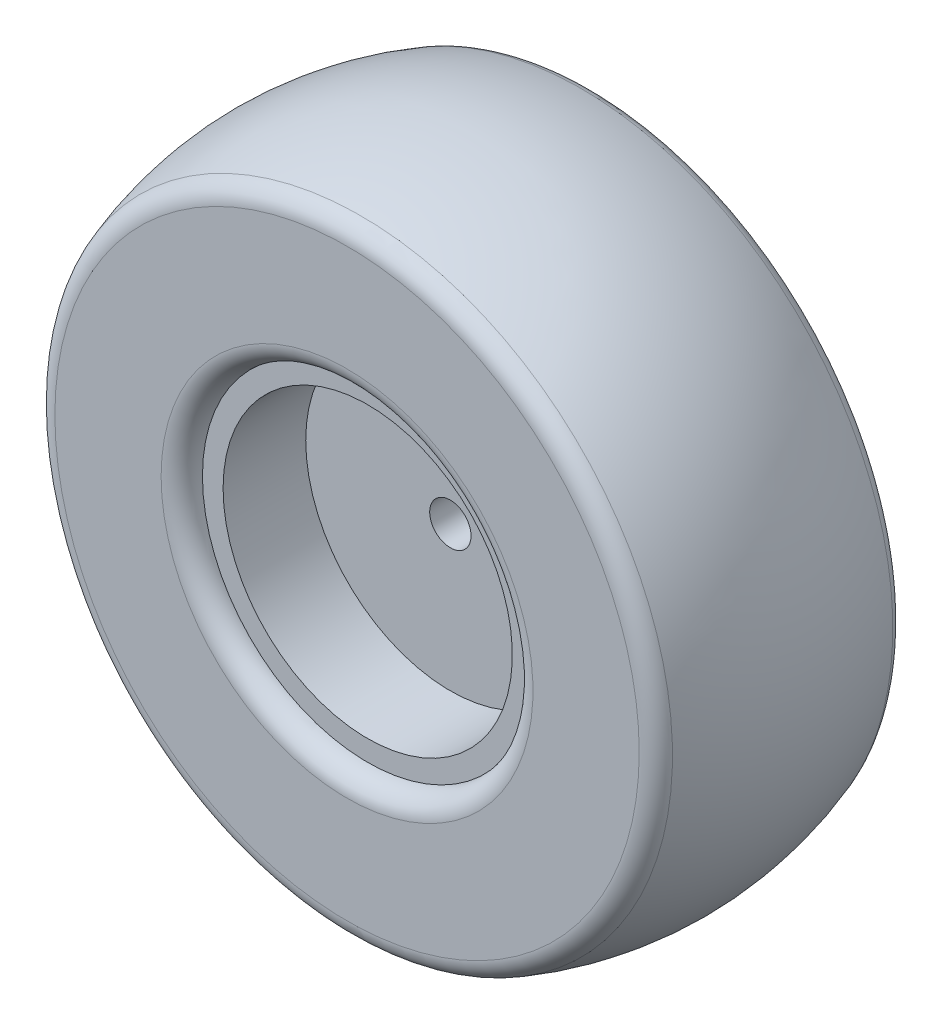
SolidWorks part; units mm, degrees
material "Rubber"
ref_plane "Front Plane" through (0, 0, 0) normal (0, 0, 1) x (1, 0, 0)
ref_plane "Top Plane" through (0, 0, 0) normal (0, 1, 0) x (1, 0, 0)
ref_plane "Right Plane" through (0, 0, 0) normal (1, 0, 0) x (0, 0, -1)
sketch "Sketch1" plane through (0, 0, 0) normal (0, 1, 0) x (1, 0, 0)
  line L0 (0, 0) -> (0, -38.1) construction
  line L1 (0, 0) -> (-101.6, 0) construction
  line L2 (-89.8026, -38.1) -> (-57.15, -38.1)
  line L5 (-101.6, 0) -> (-50.8, 0) construction
  line L6 (-50.8, 31.75) -> (-50.8, -31.75)
  line L7 (-89.8026, 38.1) -> (-57.15, 38.1)
  arc A0 (-95.7894, 33.8667) -> (-95.7894, -33.8667) centre (0, 0) ccw
  arc A1 (-89.8026, -38.1) -> (-95.7894, -33.8667) centre (-89.8026, -31.75) cw
  arc A2 (-57.15, -38.1) -> (-50.8, -31.75) centre (-57.15, -31.75) ccw
  arc A3 (-57.15, 38.1) -> (-50.8, 31.75) centre (-57.15, 31.75) cw
  arc A4 (-89.8026, 38.1) -> (-95.7894, 33.8667) centre (-89.8026, 31.75) ccw
  dimension "D1" = 76.2
  dimension "D4" = 6.35
  dimension "D5" = 6.35
  dimension "D3" = 50.8
revolve "Revolve1" add sketch "Sketch1" angle 360 about L0
sketch "Sketch2" plane through (0, 0, 0) normal (0, 1, 0) x (1, 0, 0)
  line L0 (-50.8, 31.75) -> (-44.45, 31.75)
  line L1 (-50.8, 31.75) -> (50.8, 31.75) construction
  line L2 (-44.45, 31.75) -> (-44.45, 6.35)
  line L3 (-57.15, 38.1) -> (-89.8026, 38.1)
  line L4 (-50.8, -31.75) -> (-50.8, 31.75)
  line L5 (-89.8026, -38.1) -> (-57.15, -38.1)
  line L6 (-57.15, 38.1) -> (-89.8026, 38.1)
  line L7 (-50.8, -31.75) -> (-50.8, 31.75)
  line L8 (-89.8026, -38.1) -> (-57.15, -38.1)
  line L9 (-44.45, 6.35) -> (0, 6.35)
  line L10 (0, 6.35) -> (0, -6.35)
  line L12 (-44.45, -6.35) -> (0, -6.35)
  line L13 (-44.45, -31.75) -> (-44.45, -6.35)
  line L15 (-50.8, -31.75) -> (-44.45, -31.75)
  line L16 (0, 0) -> (-101.6, 0) construction
  arc A5 (-89.8026, 38.1) -> (-95.7894, 33.8667) centre (-89.8026, 31.75) ccw
  arc A6 (-50.8, 31.75) -> (-57.15, 38.1) centre (-57.15, 31.75) ccw
  arc A7 (-57.15, -38.1) -> (-50.8, -31.75) centre (-57.15, -31.75) ccw
  arc A8 (-95.7894, -33.8667) -> (-89.8026, -38.1) centre (-89.8026, -31.75) ccw
  arc A9 (-95.7894, 33.8667) -> (-95.7894, -33.8667) centre (0, 0) ccw
  arc A10 (-89.8026, 38.1) -> (-95.7894, 33.8667) centre (-89.8026, 31.75) ccw
  arc A11 (-50.8, 31.75) -> (-57.15, 38.1) centre (-57.15, 31.75) ccw
  arc A12 (-57.15, -38.1) -> (-50.8, -31.75) centre (-57.15, -31.75) ccw
  arc A13 (-95.7894, -33.8667) -> (-89.8026, -38.1) centre (-89.8026, -31.75) ccw
  arc A14 (-95.7894, 33.8667) -> (-95.7894, -33.8667) centre (0, 0) ccw
  dimension "D2" = 12.7
  dimension "D3" = 6.35
  dimension "D1" = 0
revolve "Revolve2" add sketch "Sketch2" angle 360 about L0
sketch "Sketch3" plane through (0, 0, 6.35) normal (0, 0, 1) x (1, 0, 0)
  circle A0 centre (0, 0) radius 6.35
  dimension "D1" = 12.7
extrude "Cut-Extrude1" cut sketch "Sketch3" against normal through all both and the other way through all
